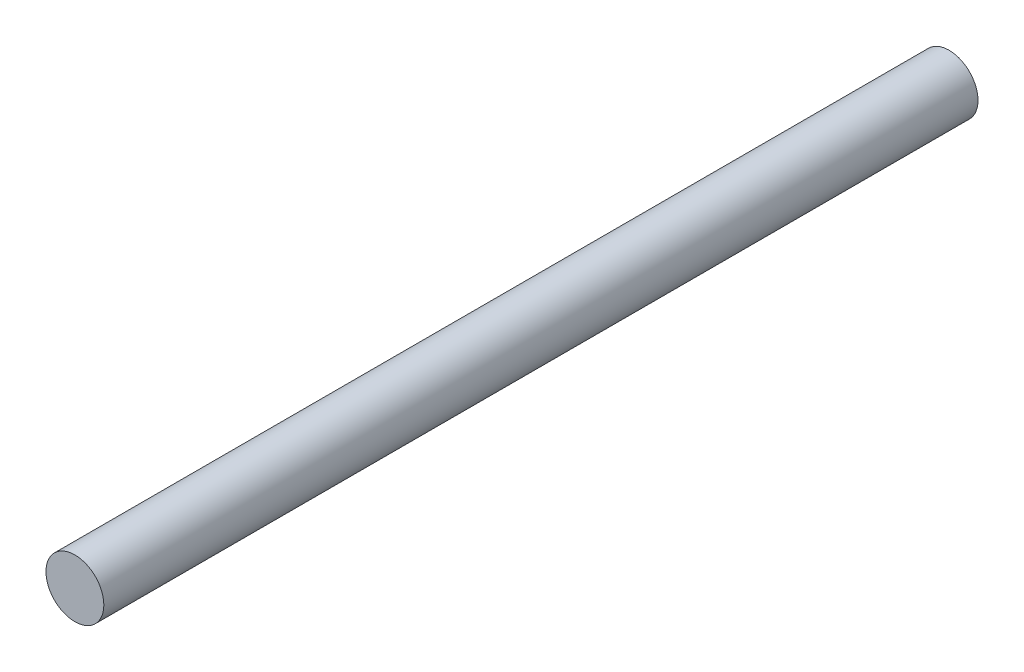
SolidWorks part; units mm, degrees
ref_plane "Front Plane" through (0, 0, 0) normal (0, 0, 1) x (1, 0, 0)
ref_plane "Top Plane" through (0, 0, 0) normal (0, 1, 0) x (1, 0, 0)
ref_plane "Right Plane" through (0, 0, 0) normal (1, 0, 0) x (0, 0, -1)
sketch "Sketch1" plane through (0, 0, 0) normal (0, 0, 1) x (1, 0, 0)
  circle A0 centre (0, 0) radius 12.5
  dimension "D1" = 25
extrude "Boss-Extrude1" add sketch "Sketch1" along normal blind 365
sketch "Sketch2" plane through (0, 0, 365) normal (0, 0, 1) x (1, 0, 0)
  circle A0 centre (0, 0) radius 12.5
extrude "Boss-Extrude2" add sketch "Sketch2" along normal blind 12.5
